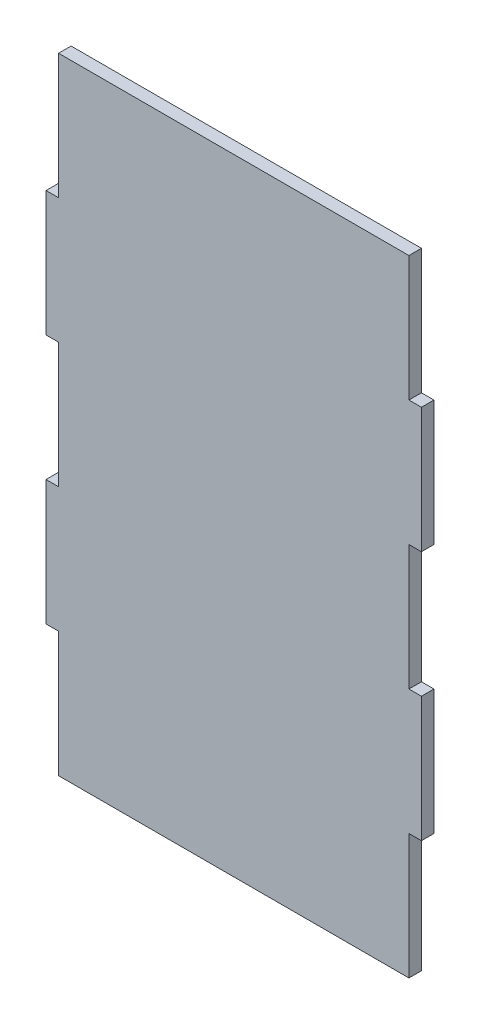
SolidWorks part; units mm, degrees
ref_plane "Front Plane" through (0, 0, 0) normal (0, 0, 1) x (1, 0, 0)
ref_plane "Top Plane" through (0, 0, 0) normal (0, 1, 0) x (1, 0, 0)
ref_plane "Right Plane" through (0, 0, 0) normal (1, 0, 0) x (0, 0, -1)
sketch "Sketch1" plane through (0, 0, 0) normal (0, 0, 1) x (1, 0, 0)
  line L1 (0, 0) -> (76.2, 0)
  line L2 (0, 0) -> (0, 127)
  line L3 (0, 127) -> (76.2, 127)
  line L4 (76.2, 0) -> (76.2, 127)
  dimension "D1" = 76.2
  dimension "D2" = 127
extrude "Boss-Extrude1" add sketch "Sketch1" along normal blind 2.54 contours L4 L3 L2 L1
sketch "Sketch2" plane through (0, 0, 2.54) normal (0, 0, 1) x (1, 0, 0)
  line L1 (0, 127) -> (2.54, 127)
  line L2 (0, 127) -> (0, 101.6)
  line L3 (0, 101.6) -> (2.54, 101.6)
  line L4 (2.54, 127) -> (2.54, 101.6)
  dimension "D1" = 2.54
  dimension "D2" = 25.4
extrude "Cut-Extrude1" cut sketch "Sketch2" against normal through all contours L2 L1 L4 L3
sketch "Sketch3" plane through (0, 0, 2.54) normal (0, 0, 1) x (1, 0, 0)
  line L1 (76.2, 127) -> (73.66, 127)
  line L2 (76.2, 127) -> (76.2, 101.6)
  line L3 (76.2, 101.6) -> (73.66, 101.6)
  line L4 (73.66, 127) -> (73.66, 101.6)
  dimension "D1" = 2.54
  dimension "D2" = 25.4
sketch "Sketch4" plane through (0, 0, 2.54) normal (0, 0, 1) x (1, 0, 0)
  line L0 (0, 0) -> (0, 101.6) construction
  line L1 (0, 0) -> (2.54, 0)
  line L2 (0, 0) -> (0, 25.4)
  line L3 (0, 25.4) -> (2.54, 25.4)
  line L4 (2.54, 0) -> (2.54, 25.4)
  line L5 (76.2, 0) -> (73.66, 0)
  line L6 (76.2, 0) -> (76.2, 25.4)
  line L7 (76.2, 25.4) -> (73.66, 25.4)
  line L8 (73.66, 0) -> (73.66, 25.4)
  line L9 (0, 76.2) -> (2.54, 76.2)
  line L10 (0, 76.2) -> (0, 50.8)
  line L11 (0, 50.8) -> (2.54, 50.8)
  line L12 (2.54, 76.2) -> (2.54, 50.8)
  line L13 (0, 101.6) -> (2.54, 101.6) construction
  line L14 (76.2, 0) -> (76.2, 127) construction
  line L15 (76.2, 50.8) -> (73.66, 50.8)
  line L16 (76.2, 50.8) -> (76.2, 76.2)
  line L17 (76.2, 76.2) -> (73.66, 76.2)
  line L18 (73.66, 50.8) -> (73.66, 76.2)
  dimension "D1" = 25.4
  dimension "D2" = 2.54
  dimension "D3" = 2.54
  dimension "D4" = 25.4
  dimension "D5" = 2.54
  dimension "D6" = 25.4
  dimension "D7" = 25.4
  dimension "D8" = 2.54
extrude "Cut-Extrude3" cut sketch "Sketch4" against normal through all contours L2 L1 L4 L3 | L10 L9 L12 L11 | L16 L15 L18 L17 | L6 L5 L8 L7
extrude "Cut-Extrude4" cut sketch "Sketch3" against normal through all contours L3 L4 L1 L2
equation "\"D1@Sketch2\" = \"Matterial_Thickness\""
equation "\"D2@Sketch4\" = \"Matterial_Thickness\""
equation "\"D1@Boss-Extrude1\" = \"Matterial_Thickness\""
equation "\"Matterial_Thickness\"= \"GMaterial\""
equation "\"D5@Sketch4\"=\"Matterial_Thickness\""
equation "\"D1@Sketch3\"=\"Matterial_Thickness\""
equation "\"D8@Sketch4\"=\"Matterial_Thickness\""
equation "\"D3@Sketch4\"=\"Matterial_Thickness\""
equation "\"GMaterial\"= \"Foamcore\""
equation "\"MDF\" = 0.3in"
equation "\"Foamcore\"= 0.1in"
